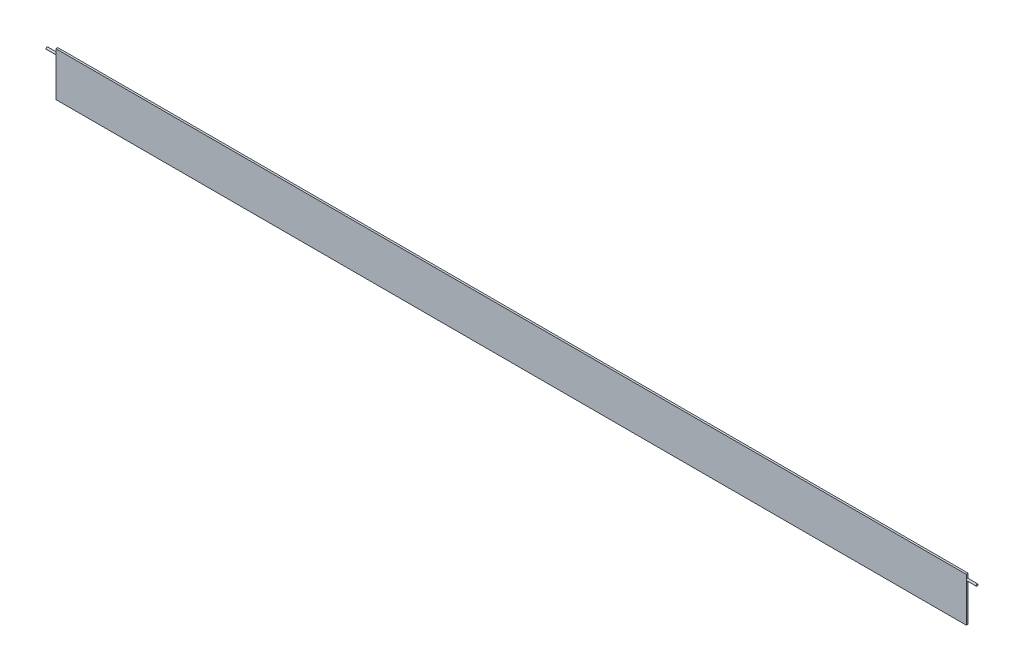
SolidWorks part; units mm, degrees
material "PP Copolymer"
ref_plane "Front Plane" through (0, 0, 0) normal (0, 0, 1) x (1, 0, 0)
ref_plane "Top Plane" through (0, 0, 0) normal (0, 1, 0) x (1, 0, 0)
ref_plane "Right Plane" through (0, 0, 0) normal (1, 0, 0) x (0, 0, -1)
sketch "Sketch1" plane through (0, 0, 0) normal (0, 0, 1) x (1, 0, 0)
  line L5 (590.55, -28.575) -> (-590.55, -28.575)
  line L6 (590.55, -28.575) -> (590.55, 28.575)
  line L7 (590.55, 28.575) -> (-590.55, 28.575)
  line L8 (-590.55, -28.575) -> (-590.55, 28.575)
  line L9 (590.55, -28.575) -> (-590.55, 28.575) construction
  line L10 (590.55, 28.575) -> (-590.55, -28.575) construction
  point P0 (0, 0)
  dimension "D1" = 1181.1
  dimension "D2" = 57.15
extrude "Boss-Extrude1" add sketch "Sketch1" along normal mid plane 2.54
sketch "Sketch2" plane through (-590.55, 0, 0) normal (-1, 0, 0) x (0, 0, 1)
  line L0 (1.27, 28.575) -> (-1.27, 28.575) construction
  circle A0 centre (0, 22.225) radius 1.27
  point P2 (0, 0)
  dimension "D1" = 2.54
  dimension "D2" = 6.35
extrude "Boss-Extrude2" add sketch "Sketch2" along normal blind 12.7 and the other way offset from surface (1193.8 mm away) 12.7 other way up to face at (590.55, 0, 0)
